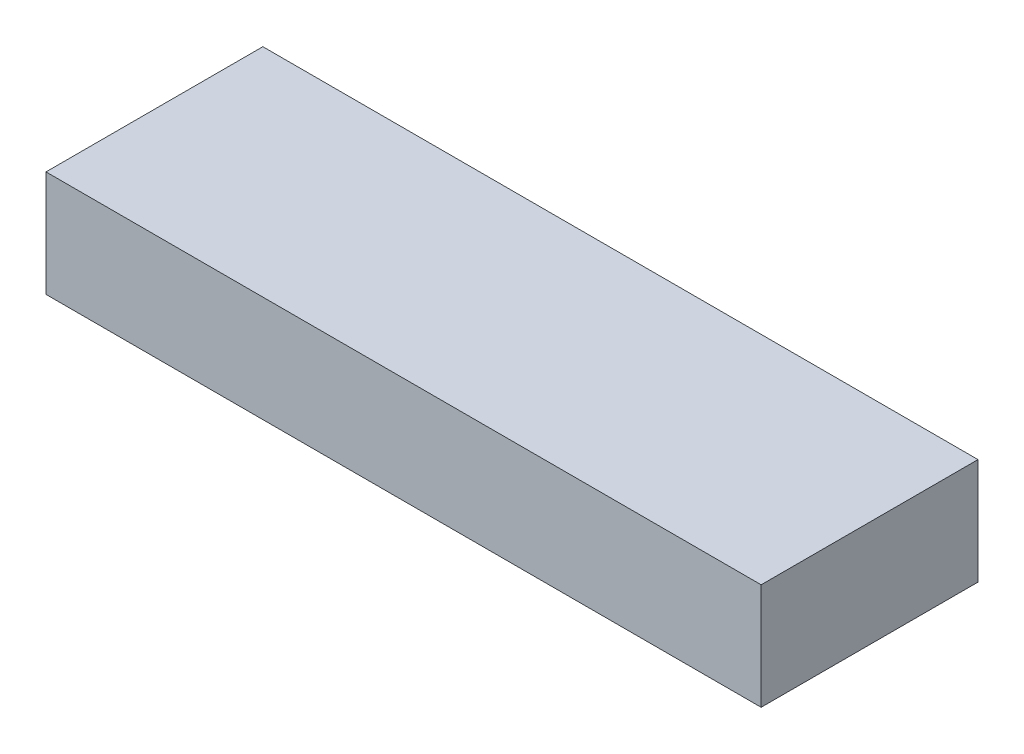
SolidWorks part; units mm, degrees
ref_plane "Front" through (0, 0, 0) normal (0, 0, 1) x (1, 0, 0)
ref_plane "Top" through (0, 0, 0) normal (0, 1, 0) x (1, 0, 0)
ref_plane "Right" through (0, 0, 0) normal (1, 0, 0) x (0, 0, -1)
sketch "Sketch1" plane through (0, 0, 0) normal (0, 1, 0) x (1, 0, 0)
  line L1 (-77.5, 23.5) -> (77.5, 23.5)
  line L2 (-77.5, 23.5) -> (-77.5, -23.5)
  line L3 (-77.5, -23.5) -> (77.5, -23.5)
  line L4 (77.5, 23.5) -> (77.5, -23.5)
  line L5 (-77.5, 23.5) -> (77.5, -23.5) construction
  line L6 (-77.5, -23.5) -> (77.5, 23.5) construction
  point P0 (0, 0)
  dimension "D1" = 155
  dimension "D2" = 47
extrude "Boss-Extrude1" add sketch "Sketch1" along normal blind 23
